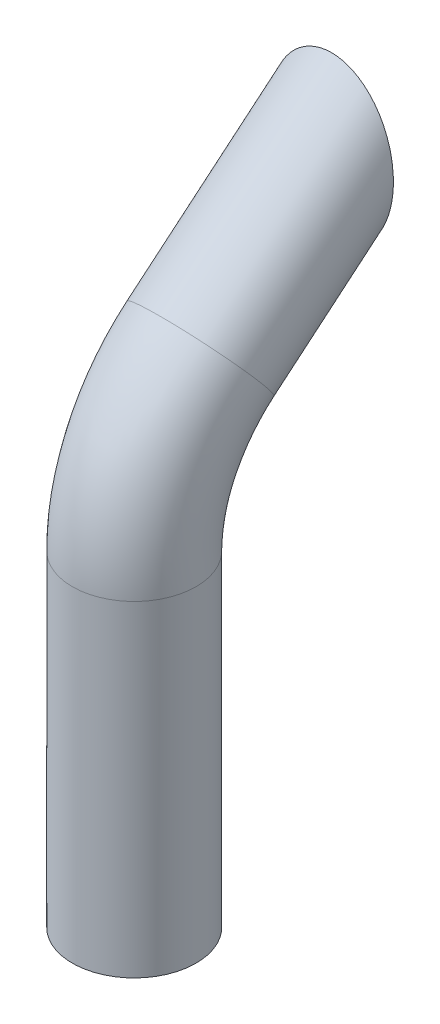
SolidWorks part; units mm, degrees
ref_plane "Front Plane" through (0, 0, 0) normal (0, 0, 1) x (1, 0, 0)
ref_plane "Top Plane" through (0, 0, 0) normal (0, 1, 0) x (1, 0, 0)
ref_plane "Right Plane" through (0, 0, 0) normal (1, 0, 0) x (0, 0, -1)
sketch "Sketch1" plane through (0, 0, 0) normal (1, 0, 0) x (0, 0, -1)
  line L0 (0, 0) -> (-82.7576, -69.4418)
  line L1 (-114.9067, -138.3858) -> (-114.9067, -296.4181)
  arc A0 (-82.7576, -69.4418) -> (-114.9067, -138.3858) centre (-24.9067, -138.3858) ccw
  point P6 (-114.9067, -96.4181)
  dimension "D4" = 90
  dimension "D1" = 150
  dimension "D2" = 200
  dimension "D3" = 130
ref_plane "Plane1" through (0, 0, 0) normal (0, -0.6428, 0.766) x (1, 0, 0)
sketch "Sketch2" plane through (0, 0, 0) normal (0, -0.6428, 0.766) x (1, 0, 0)
  circle A0 centre (0, 0) radius 30
  dimension "D1" = 60
sweep "Sweep-Thin1" add profiles "Sketch2" path "Sketch1" parameters "D1"=3
sketch "Sketch3" plane through (0, 0, 0) normal (1, 0, 0) x (0, 0, -1)
  line L5 (-19.2836, 22.9813) -> (59.1617, 22.9813)
  line L6 (-19.2836, 22.9813) -> (-19.2836, -65.1074)
  line L7 (-19.2836, -65.1074) -> (59.1617, -65.1074)
  line L8 (59.1617, 22.9813) -> (59.1617, -65.1074)
extrude "Cut-Extrude2" cut sketch "Sketch3" against normal mid plane 90
